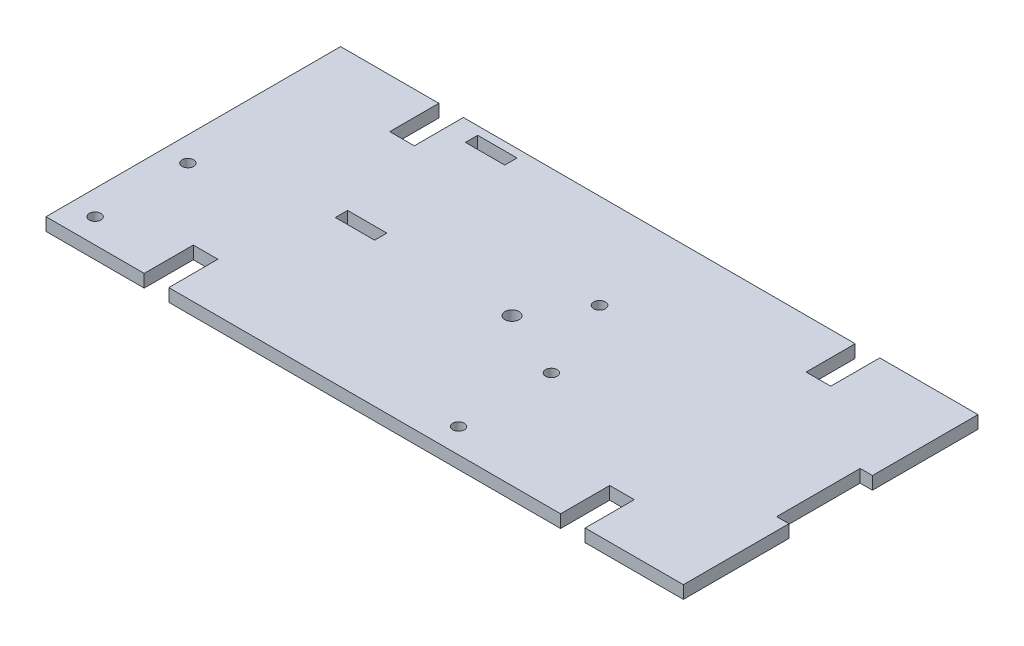
SolidWorks part; units mm, degrees
material "Cedar"
ref_plane "Front Plane" through (0, 0, 0) normal (0, 0, 1) x (1, 0, 0)
ref_plane "Top Plane" through (0, 0, 0) normal (0, 1, 0) x (1, 0, 0)
ref_plane "Right Plane" through (0, 0, 0) normal (1, 0, 0) x (0, 0, -1)
sketch "Sketch1" plane through (0, 0, 0) normal (0, 1, 0) x (1, 0, 0)
  line L0 (-164.846, 76.2) -> (-139.446, 76.2)
  line L9 (-139.446, 76.2) -> (-139.446, 63.5)
  line L10 (-139.446, 63.5) -> (-133.096, 63.5)
  line L11 (-133.096, 63.5) -> (-133.096, 76.2)
  line L12 (-133.096, 76.2) -> (-31.75, 76.2)
  line L13 (-31.75, 76.2) -> (-31.75, 63.5)
  line L14 (-31.75, 63.5) -> (-25.4, 63.5)
  line L15 (-25.4, 63.5) -> (-25.4, 76.2)
  line L16 (-25.4, 76.2) -> (0, 76.2)
  line L17 (0, 76.2) -> (0, 48.895)
  line L21 (0, 27.305) -> (0, 0)
  line L22 (0, 0) -> (-25.4, 0)
  line L23 (-25.4, 0) -> (-25.4, 12.7)
  line L24 (-25.4, 12.7) -> (-31.75, 12.7)
  line L25 (-31.75, 12.7) -> (-31.75, 0)
  line L26 (-31.75, 0) -> (-133.096, 0)
  line L27 (-133.096, 0) -> (-133.096, 12.7)
  line L28 (-133.096, 12.7) -> (-139.446, 12.7)
  line L29 (-139.446, 12.7) -> (-139.446, 0)
  line L30 (-139.446, 0) -> (-164.846, 0)
  line L31 (-164.846, 0) -> (-164.846, 27.305)
  line L33 (-164.846, 27.305) -> (-164.846, 48.895)
  line L35 (-164.846, 48.895) -> (-164.846, 76.2)
  line L36 (-82.423, 76.2) -> (-82.423, 0) construction
  line L37 (0, 48.895) -> (-3.175, 48.895)
  line L39 (0, 27.305) -> (-3.175, 27.305)
  line L40 (-3.175, 48.895) -> (-3.175, 27.305)
  line L41 (-164.846, 38.1) -> (-3.175, 38.1) construction
  circle A0 centre (-82.423, 38.1) radius 1.8288
  dimension "D8" = 3.6576
  dimension "D1" = 76.2
  dimension "D2" = 164.846
  dimension "D3" = 21.59
  dimension "D4" = 6.35
  dimension "D5" = 12.7
  dimension "D6" = 3.175
  dimension "D7" = 25.4
extrude "Boss-Extrude1" add sketch "Sketch1" along normal blind 3.302
sketch "Sketch2" plane through (0, 3.302, 0) normal (0, 1, 0) x (1, 0, 0)
  line L0 (-133.096, 0) -> (-31.75, 0) construction
  line L1 (-164.846, 76.2) -> (-164.846, 0) construction
  circle A0 centre (-158.496, 30.35) radius 1.5
  circle A1 centre (-158.496, 6.35) radius 1.5
  circle A2 centre (-64.496, 6.35) radius 1.5
  circle A3 centre (-64.496, 30.35) radius 1.5
  dimension "D1" = 3
  dimension "D2" = 94
  dimension "D3" = 24
  dimension "D4" = 6.35
  dimension "D5" = 6.35
extrude "Cut-Extrude1" cut sketch "Sketch2" against normal through all
sketch "Sketch3" plane through (0, 3.302, 0) normal (0, 1, 0) x (1, 0, 0)
  line L0 (-42.343, 51.7237) -> (-164.846, 51.7237) construction
  line L1 (-127.2493, 67.3084) -> (-127.2493, 40.4047) construction
  line L2 (-127.2493, 40.4047) -> (-117.0893, 40.4047)
  line L3 (-127.2493, 40.4047) -> (-127.2493, 37.2297)
  line L4 (-127.2493, 37.2297) -> (-117.0893, 37.2297)
  line L5 (-117.0893, 40.4047) -> (-117.0893, 37.2297)
  line L6 (-127.2493, 74.0597) -> (-117.0893, 74.0597)
  line L7 (-127.2493, 74.0597) -> (-127.2493, 70.8847)
  line L8 (-127.2493, 70.8847) -> (-117.0893, 70.8847)
  line L9 (-117.0893, 74.0597) -> (-117.0893, 70.8847)
  line L10 (-164.846, 76.2) -> (-164.846, 0) construction
  circle A0 centre (-73.406, 51.7237) radius 1.524
  dimension "D5" = 3.048
  dimension "D1" = 91.44
  dimension "D2" = 30.48
  dimension "D3" = 10.16
  dimension "D4" = 3.175
extrude "Cut-Extrude2" cut sketch "Sketch3" against normal through all
